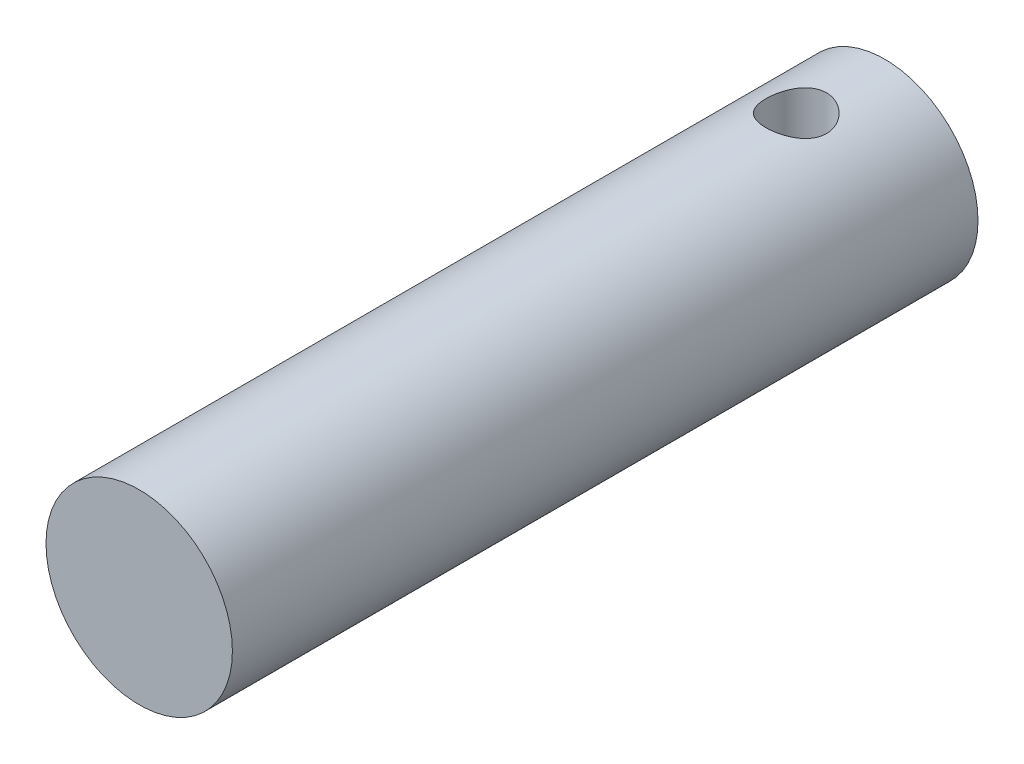
SolidWorks part; units mm, degrees
ref_plane "前视基准面" through (0, 0, 0) normal (0, 0, 1) x (1, 0, 0)
ref_plane "上视基准面" through (0, 0, 0) normal (0, 1, 0) x (1, 0, 0)
ref_plane "右视基准面" through (0, 0, 0) normal (1, 0, 0) x (0, 0, -1)
sketch "草图1" plane through (0, 0, 0) normal (0, 0, 1) x (1, 0, 0)
  circle A0 centre (0, 0) radius 10
  dimension "D1" = 20
extrude "凸台-拉伸1" add sketch "草图1" along normal blind 80
sketch "草图2" plane through (0, 0, 0) normal (0, 1, 0) x (1, 0, 0)
  line L0 (0, 19.453) -> (0, -26.2878) construction
  line L1 (10, 0) -> (-10, 0) construction
  circle A0 centre (0, -9.5) radius 3.25
  dimension "D1" = 6.5
  dimension "D2" = 9.5
extrude "切除-拉伸1" cut sketch "草图2" against normal mid plane 420
